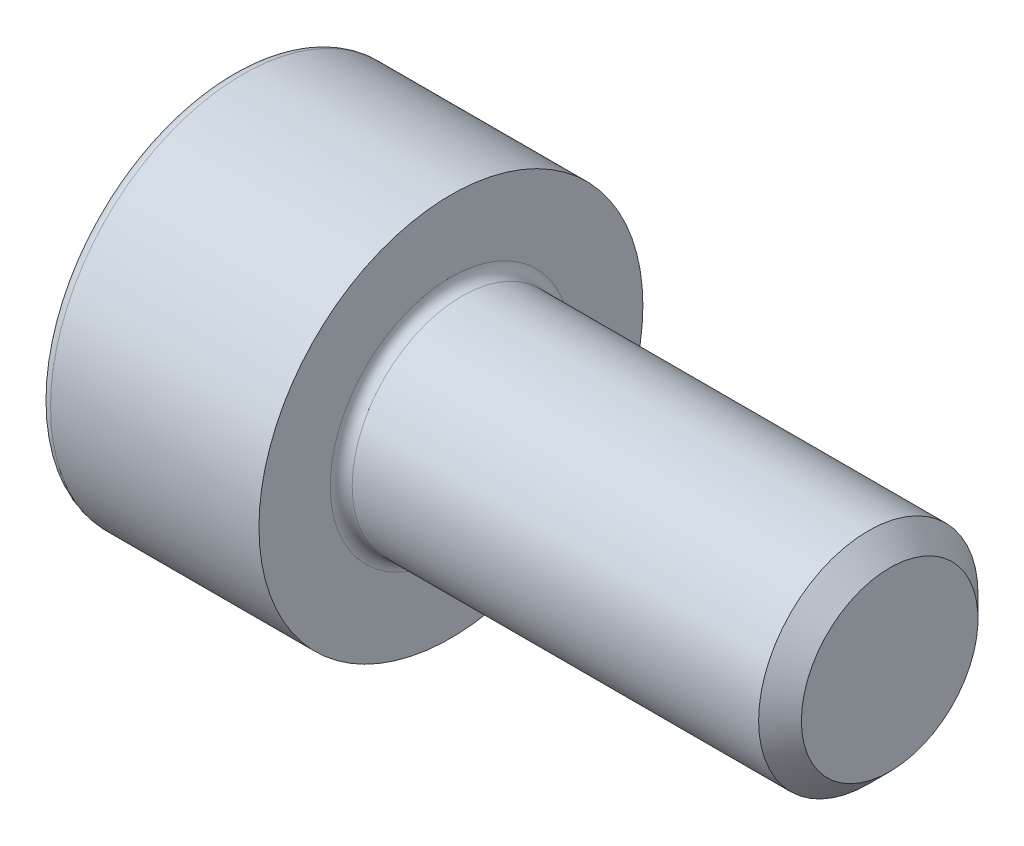
SolidWorks part; units mm, degrees
ref_plane "Plane1" through (0, 0, 0) normal (0, 0, 1) x (1, 0, 0)
ref_plane "Plane2" through (0, 0, 0) normal (0, 1, 0) x (1, 0, 0)
ref_plane "Plane3" through (0, 0, 0) normal (1, 0, 0) x (0, 0, -1)
revolve "Base-Revolve" add sketch "BodySke"
sketch "BodySke" plane through (0, 0, 0) normal (0, 0, 1) x (1, 0, 0)
  line L0 (0, 0) -> (0, 3.5)
  line L1 (0, 3.5) -> (4, 3.5)
  line L2 (4, 3.5) -> (4, 2)
  line L3 (4, 2) -> (11.61, 2)
  line L4 (12, 1.61) -> (12, 0)
  line L5 (12, 0) -> (0, 0)
  line L6 (-31.75, 0) -> (127, 0) construction
  line L8 (12, 1.61) -> (11.61, 2)
  line L10 (12, -1.61) -> (11.61, -2) construction
  line L11 (4.7, 9.525) -> (4.7, 3.175) construction
  line L12 (4, 9.525) -> (4, 3.175) construction
  line L13 (-48, 9.525) -> (-48, 3.175) construction
  dimension "Diameter" = 4
  dimension "Head_ht" = 4
  dimension "Length" = 8
  dimension "Body_ch_ang" = 45
  dimension "Head_dia" = 7
  dimension "Minor_dia" = 3.22
  dimension "Advance" = 0.7
  dimension "Thread_nom" = 8
  dimension "Thread_length" = 60
cosmetic thread "ThreadCosmetic"
fillet "Fillet1" radius 0.2 1 edges at (4, 0, 2)
fillet "Fillet2" radius 0.2 1 edges at (0, 0, 3.5)
sketch "Sketch2" plane through (0, 0, 0) normal (0, 0, 1) x (1, 0, 0)
  line L0 (0, 1.5355) -> (2, 1.5355)
  line L1 (2, 1.5355) -> (2.8865, 0)
  line L2 (-31.75, 0) -> (127, 0) construction
  line L3 (2.8865, 0) -> (0, 0)
  line L4 (0, 0) -> (0, 1.5355)
  line L6 (0, 0) -> (47.625, 0) construction
  dimension "D1" = 1.5355
  dimension "D2" = 60
  dimension "Depth" = 2
revolve "Hex-PreBroach" cut sketch "Sketch2" angle 360 about L6
sketch "Sketch3" plane through (0, 0, 0) normal (-1, 0, 0) x (0, 0.5, 0.866)
  line L0 (0.8865, 1.5355) -> (-0.8865, 1.5355)
  line L1 (-0.8865, 1.5355) -> (-1.773, 0)
  line L2 (0.8865, 1.5355) -> (1.773, 0)
  line L3 (0.8865, -1.5355) -> (1.773, 0)
  line L4 (0.8865, -1.5355) -> (-0.8865, -1.5355)
  line L5 (-0.8865, -1.5355) -> (-1.773, 0)
  dimension "D1" = 1.5355
  dimension "D2" = 1.5355
  dimension "Hex_size" = 3.071
extrude "Hex" cut sketch "Sketch3" against normal blind 2
sketch "ThdSchSke" plane through (0, 0, 0) normal (0, 0, 1) x (1, 0, 0)
  line L0 (6.1, -1.61) -> (5.8269, -2)
  line L1 (6.1, -1.61) -> (6.3731, -2)
  line L2 (6.3731, -2) -> (6.3731, -2.5)
  line L3 (-3.175, 0) -> (5.1513, 0) construction
  line L4 (0, 3.3) -> (0, -3.3) construction
  line L5 (6.3731, -2.5) -> (5.8269, -2.5)
  line L6 (5.8269, -2.5) -> (5.8269, -2)
  dimension "Thread_minor" = 3.22
  dimension "Diameter" = 4
  dimension "Start" = 6.1
  dimension "SideAngle" = 55
  dimension "VeeAngle" = 70
  dimension "Overcut" = 5
revolve "ThreadSchematic" cut sketch "ThdSchSke" angle 360 about L3
pattern_linear "ThdSchPat"
equation "\"D2@Sketch3\" = \"Hex_size@Sketch3\" / 2"
equation "\"D1@Sketch3\" = \"Hex_size@Sketch3\" / 2"
equation "\"D1@Sketch2\" = \"Hex_size@Sketch3\" / 2"
equation "\"Thread_minor@ThreadCosmetic\"  =  \"Minor_dia@BodySke\""
equation "\"Depth@Sketch2\" =  \"Key_eng@Hex\""
equation "\"Thread_length@ThreadCosmetic\" = ((sgn( (\"Length@BodySke\" - \"Advance@BodySke\" * 3.0) - \"Thread_nom@BodySke\" )-1)*( (\"Length@BodySke\" - \"Advance@BodySke\" * 3.0) - \"Thread_nom@BodySke\" ))/-2+ \"Thread_nom@BodySke\""
equation "\"Thread_minor@ThdSchSke\" = \"Minor_dia@BodySke\""
equation "\"Diameter@ThdSchSke\" = \"Diameter@BodySke\""
equation "\"Overcut@ThdSchSke\" = \"Diameter@BodySke\" * 1.25"
equation "\"Start@ThdSchSke\" = \"Head_ht@BodySke\" + \"Length@BodySke\" - \"Thread_length@ThreadCosmetic\"  '---Non-countersunk---"
equation "\"Num_threads@ThdSchPat\" = int( \"Thread_length@ThreadCosmetic\" / \"Advance@BodySke\" + 0.999 )  + 1"
equation "\"Advance@ThdSchPat\" = \"Thread_length@ThreadCosmetic\" /  (\"Num_threads@ThdSchPat\" - 1) 'relax it"
equation "\"Num_threads@ThdSchPat\" = \"Num_threads@ThdSchPat\" - sgn( \"Num_threads@ThdSchPat\" - 1) '---chamfered tips only---"
